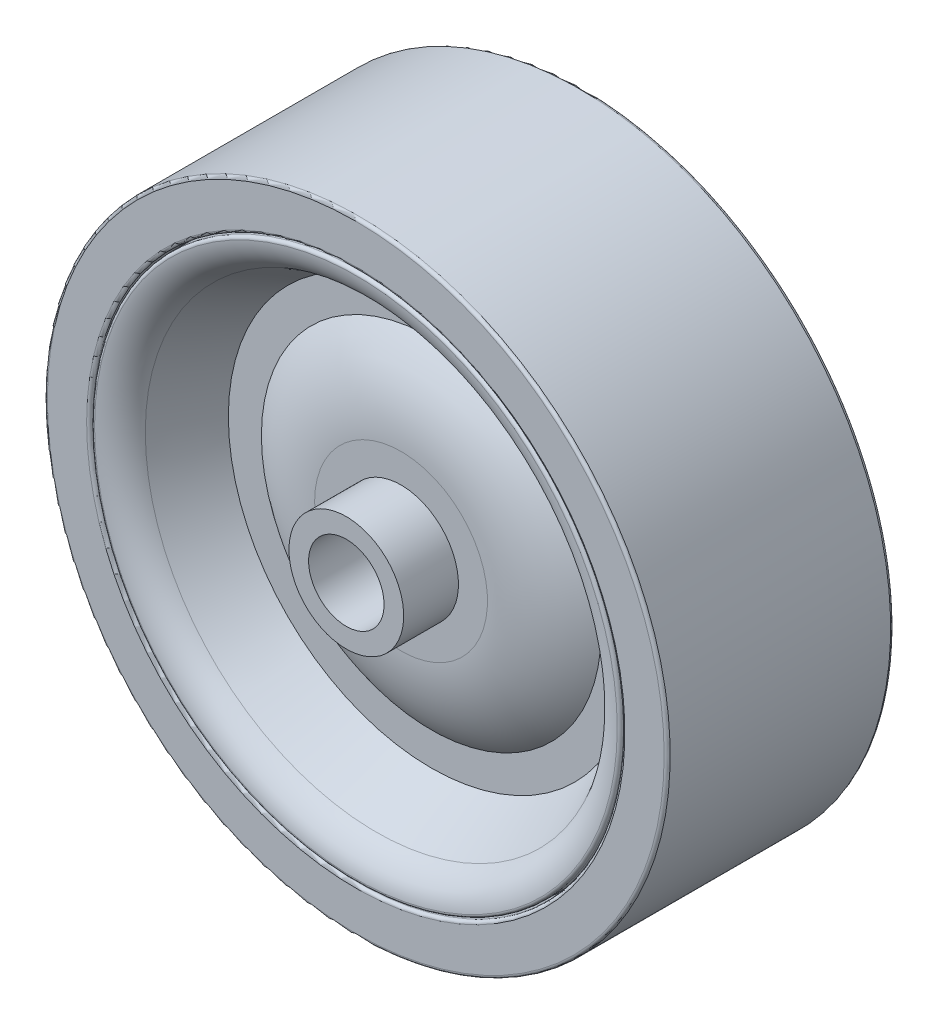
SolidWorks part; units mm, degrees
ref_plane "Front" through (0, 0, 0) normal (0, 0, 1) x (1, 0, 0)
ref_plane "Top" through (0, 0, 0) normal (0, 1, 0) x (1, 0, 0)
ref_plane "Right" through (0, 0, 0) normal (1, 0, 0) x (0, 0, -1)
sketch "Sketch1" plane through (0, 0, 0) normal (1, 0, 0) x (0, 0, -1)
  line L0 (0, 26.1937) -> (9.525, 26.1937)
  line L1 (0, 26.1937) -> (0, 3.175)
  line L2 (0, 3.175) -> (10.3188, 3.175)
  line L3 (10.3188, 3.175) -> (10.3187, 4.826)
  line L4 (10.3187, 4.826) -> (5.715, 4.826)
  line L5 (10.3187, 4.826) -> (10.3188, -4.826) construction
  line L6 (10.3188, 3.175) -> (10.3188, -3.175) construction
  line L7 (3.175, 17.0656) -> (7.7963, 19.4303)
  line L8 (0, 26.1937) -> (0, -26.1937) construction
  line L9 (10.3187, 0) -> (-10.3187, 0) construction
  line L10 (9.525, 26.1937) -> (-9.525, 26.1937) construction
  line L11 (5.715, 7.2695) -> (5.715, 4.826)
  line L12 (3.175, 14.2875) -> (3.175, 17.0656)
  line L13 (9.525, 26.1937) -> (9.525, 22.3837)
  line L14 (9.525, 22.3837) -> (6.985, 22.3837)
  line L15 (6.985, 22.3837) -> (6.985, 22.2568)
  line L16 (6.985, 22.2568) -> (9.525, 22.2568)
  line L19 (5.715, 4.826) -> (-5.715, 4.826) construction
  line L20 (3.175, 15.6766) -> (-3.175, 15.6766) construction
  arc A0 (9.525, 22.2568) -> (7.7963, 19.4303) centre (6.35, 22.2568) cw
  arc A2 (3.175, 14.2875) -> (5.715, 7.2695) centre (-5.2505, 7.2695) cw
  point P27 (0, 4.826)
  point P31 (0, 15.6766)
  dimension "D2" = 3.81
  dimension "D8" = 3.175
  dimension "D1" = 9.652
  dimension "D3" = 11.43
  dimension "D4" = 6.35
  dimension "D5" = 14.2875
  dimension "D6" = 2.7781
  dimension "D7" = 2.4435
  dimension "Bore Dia" = 6.35
  dimension "Hub Lg" = 20.6375
  dimension "Wheel Wd" = 19.05
  dimension "Wheel Dia" = 52.3875
  dimension "D9" = 0.127
  dimension "D10" = 2.54
revolve "Revolve1" add sketch "Sketch1" angle 360 mid plane about L9
fillet "Fillet1" radius 0.254 3 edges at (-26.1937, 0, -9.525) (-22.3837, 0, -9.525) (-22.2567, 0, -9.525)
mirror "Mirror1" about plane through (0, 0, 0) normal (0, 0, 1) of bodies 109
equation "\"D1@Sketch1\" = \"Bore Dia@Sketch1\" * 1.52"
